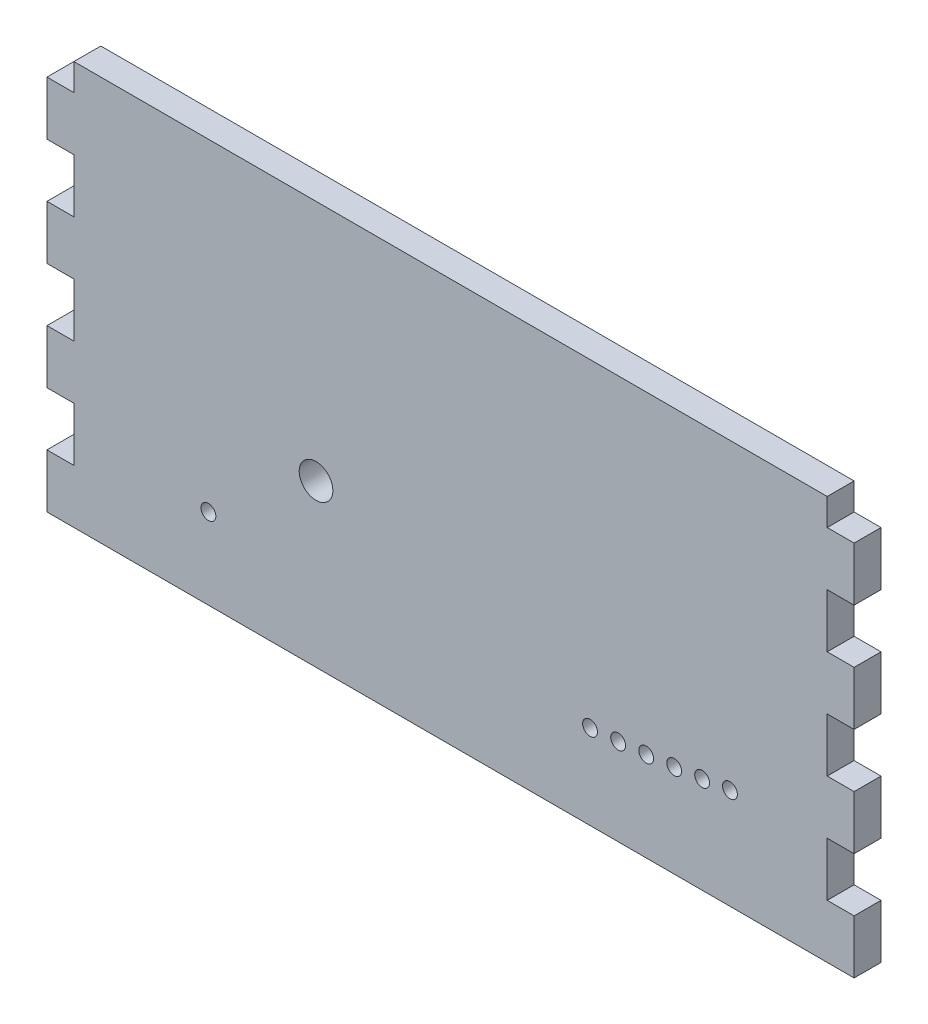
SolidWorks part; units mm, degrees
material "Pine"
ref_plane "Front Plane" through (0, 0, 0) normal (0, 0, 1) x (1, 0, 0)
ref_plane "Top Plane" through (0, 0, 0) normal (0, 1, 0) x (1, 0, 0)
ref_plane "Right Plane" through (0, 0, 0) normal (1, 0, 0) x (0, 0, -1)
sketch "Sketch1" plane through (0, 0, 0) normal (0, 0, 1) x (1, 0, 0)
  line L1 (0, 0) -> (190.5, 0)
  line L2 (0, 0) -> (0, 95.25)
  line L3 (0, 95.25) -> (190.5, 95.25)
  line L4 (190.5, 0) -> (190.5, 95.25)
  dimension "D1" = 190.5
  dimension "D2" = 95.25
extrude "Boss-Extrude1" add sketch "Sketch1" along normal blind 6.35
sketch "Sketch2" plane through (0, 0, 6.35) normal (0, 0, 1) x (1, 0, 0)
  line L0 (0, 95.25) -> (0, 0) construction
  line L1 (0, 0) -> (190.5, 0) construction
  circle A0 centre (63.5, 38.1) radius 3.9687
  dimension "D3" = 7.9375
  dimension "D1" = 63.5
  dimension "D2" = 38.1
extrude "Cut-Extrude1" cut sketch "Sketch2" against normal through all
sketch "Sketch3" plane through (0, 0, 6.35) normal (0, 0, 1) x (1, 0, 0)
  line L0 (0, 95.25) -> (0, 0) construction
  line L1 (0, 12.7) -> (6.35, 12.7)
  line L2 (0, 12.7) -> (0, 25.4)
  line L3 (0, 25.4) -> (6.35, 25.4)
  line L4 (6.35, 12.7) -> (6.35, 25.4)
  dimension "D1" = 6.35
  dimension "D2" = 12.7
  dimension "D3" = 12.7
extrude "Cut-Extrude2" cut sketch "Sketch3" against normal through all
sketch "Sketch4" plane through (0, 0, 6.35) normal (0, 0, 1) x (1, 0, 0)
  line L0 (190.5, 0) -> (190.5, 95.25) construction
  line L1 (190.5, 12.7) -> (184.15, 12.7)
  line L2 (190.5, 12.7) -> (190.5, 25.4)
  line L3 (190.5, 25.4) -> (184.15, 25.4)
  line L4 (184.15, 12.7) -> (184.15, 25.4)
  line L5 (6.35, 12.7) -> (6.35, 25.4) construction
  line L6 (0, 12.7) -> (6.35, 12.7) construction
extrude "Cut-Extrude3" cut sketch "Sketch4" against normal through all
pattern_linear "LPattern1" count 4 spacing 25.4 along (0, 1, 0) of "Cut-Extrude2", "Cut-Extrude3"
sketch "Sketch5" plane through (0, 0, 6.35) normal (0, 0, 1) x (1, 0, 0)
  line L0 (38.1, 19.05) -> (38.1, 400.05) construction
  line L1 (38.1, 400.05) -> (101.6, 400.05) construction
  line L2 (101.6, 400.05) -> (101.6, 19.05) construction
  line L3 (0, 0) -> (190.5, 0) construction
  line L4 (0, 12.7) -> (0, 0) construction
  line L5 (101.6, 400.05) -> (101.6, 19.05) construction
  line L6 (101.6, 400.05) -> (108.2494, 19.108) construction
  circle A0 centre (38.1, 19.05) radius 1.75
  circle A1 centre (101.6, 19.05) radius 1.75 construction
  circle A2 centre (108.2494, 19.108) radius 1.75 construction
  circle A3 centre (114.8967, 19.2821) radius 1.75 construction
  circle A4 centre (121.54, 19.5721) radius 1.75 construction
  circle A5 centre (128.1772, 19.9781) radius 1.75
  circle A6 centre (134.8063, 20.4998) radius 1.75
  circle A7 centre (141.4253, 21.1372) radius 1.75
  circle A8 centre (148.0322, 21.8899) radius 1.75
  circle A9 centre (154.625, 22.7579) radius 1.75
  circle A10 centre (161.2015, 23.7407) radius 1.75
  dimension "D1" = 3.5
  dimension "D2" = 381
  dimension "D3" = 400.05
  dimension "D4" = 38.1
  dimension "D5" = 101.6
  dimension "D7" = 1
  dimension "D6" = 10
extrude "Cut-Extrude4" cut sketch "Sketch5" against normal through all
